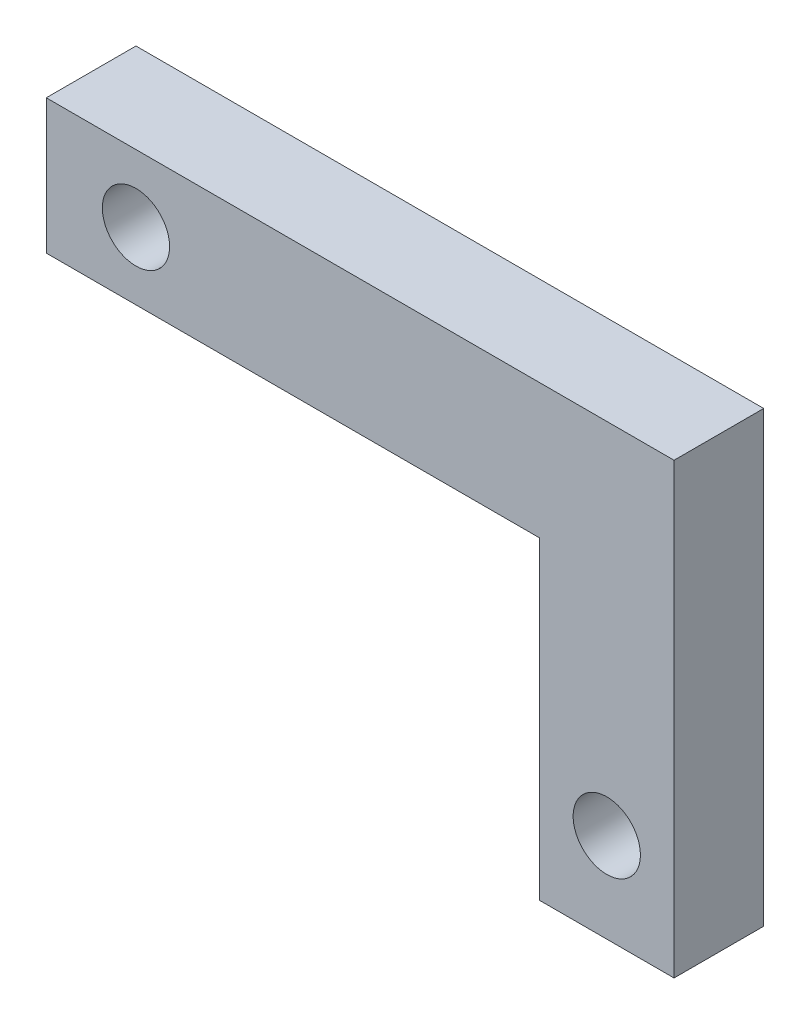
SolidWorks part; units mm, degrees
material "Pine"
ref_plane "Front Plane" through (0, 0, 0) normal (0, 0, 1) x (1, 0, 0)
ref_plane "Top Plane" through (0, 0, 0) normal (0, 1, 0) x (1, 0, 0)
ref_plane "Right Plane" through (0, 0, 0) normal (1, 0, 0) x (0, 0, -1)
sketch "Sketch1" plane through (0, 0, 0) normal (0, 0, 1) x (1, 0, 0)
  line L1 (0, 0) -> (177.8, 0)
  line L2 (0, 0) -> (0, 38.1)
  line L3 (0, 38.1) -> (177.8, 38.1)
  line L4 (177.8, 0) -> (177.8, 38.1)
  line L5 (177.8, 0) -> (139.7, 0)
  line L6 (177.8, 0) -> (177.8, -88.9)
  line L7 (177.8, -88.9) -> (139.7, -88.9)
  line L8 (139.7, 0) -> (139.7, -88.9)
  dimension "D1" = 177.8
  dimension "D2" = 38.1
  dimension "D3" = 88.9
  dimension "D4" = 38.1
extrude "Boss-Extrude1" add sketch "Sketch1" along normal blind 25.4 contours L1 L4 L3 L2 | L1 L8 L7 L6
sketch "Sketch2" plane through (0, 0, 25.4) normal (0, 0, 1) x (1, 0, 0)
  line L0 (0, 0) -> (0, 38.1) construction
  line L1 (0, 0) -> (139.7, 0) construction
  circle A0 centre (25.4, 19.05) radius 9.525
  dimension "D1" = 19.05
  dimension "D2" = 25.4
  dimension "D3" = 19.05
extrude "Cut-Extrude1" cut sketch "Sketch2" against normal through all
sketch "Sketch3" plane through (0, 0, 25.4) normal (0, 0, 1) x (1, 0, 0)
  line L0 (177.8, -88.9) -> (177.8, 38.1) construction
  line L1 (177.8, -88.9) -> (139.7, -88.9) construction
  circle A0 centre (158.75, -63.5) radius 9.525
  dimension "D1" = 19.05
  dimension "D2" = 19.05
  dimension "D3" = 25.4
extrude "Cut-Extrude2" cut sketch "Sketch3" against normal through all
